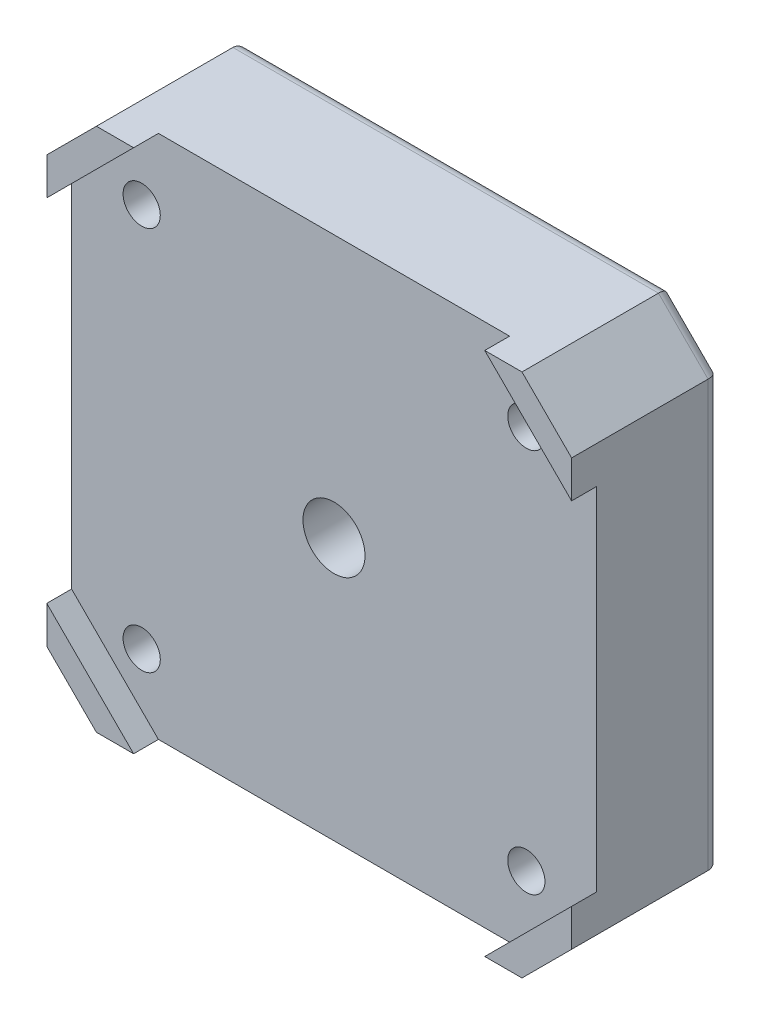
SolidWorks part; units mm, degrees
ref_plane "Ön Düzlem" through (0, 0, 0) normal (0, 0, 1) x (1, 0, 0)
ref_plane "Üst Düzlem" through (0, 0, 0) normal (0, 1, 0) x (1, 0, 0)
ref_plane "Sağ Düzlem" through (0, 0, 0) normal (1, 0, 0) x (0, 0, -1)
sketch "Çizim1" plane through (0, 0, 0) normal (0, 0, 1) x (1, 0, 0)
  line L0 (0, 38.3) -> (4, 42.3)
  line L1 (4, 42.3) -> (38.3, 42.3)
  line L2 (0, 38.3) -> (0, 4)
  line L3 (4, 0) -> (38.3, 0)
  line L4 (42.3, 38.3) -> (42.3, 4)
  line L5 (38.3, 42.3) -> (42.3, 38.3)
  line L6 (38.3, 0) -> (42.3, 4)
  line L7 (0, 4) -> (4, 0)
  point P0 (0, 42.3)
  point P1 (42.3, 0)
  point P2 (0, 0)
  point P3 (42.3, 42.3)
  dimension "D1" = 42.3
  dimension "D2" = 42.3
extrude "Yükseklik-Ekstrüzyon1" add sketch "Çizim1" along normal blind 12
sketch "Çizim2" plane through (0, 0, 12) normal (0, 0, 1) x (1, 0, 0)
  line L0 (0, 35.3) -> (7, 42.3)
  line L1 (7, 0) -> (35.3, 0)
  line L2 (0, 7) -> (0, 35.3)
  line L3 (7, 42.3) -> (35.3, 42.3)
  line L4 (42.3, 7) -> (42.3, 35.3)
  line L5 (35.3, 42.3) -> (42.3, 35.3)
  line L6 (35.3, 0) -> (42.3, 7)
  line L7 (0, 7) -> (7, 0)
  point P0 (0, 0)
  point P1 (42.3, 42.3)
  point P2 (0, 42.3)
  point P3 (42.3, 0)
  dimension "D1" = 42.3
  dimension "D2" = 42.3
extrude "Kes-Ekstrüzyon1" cut sketch "Çizim2" against normal blind 2
sketch "Çizim3" plane through (0, 0, 10) normal (0, 0, 1) x (1, 0, 0)
  line L0 (21.15, 0) -> (21.15, 42.3) construction
  line L1 (7, 0) -> (35.3, 0) construction
  line L2 (35.3, 42.3) -> (7, 42.3) construction
  line L3 (21.15, 21.15) -> (0, 21.15) construction
  line L4 (0, 35.3) -> (0, 7) construction
  line L5 (0, 21.15) -> (42.3, 21.15) construction
  line L6 (42.3, 7) -> (42.3, 35.3) construction
  line L8 (5.65, 36.65) -> (36.65, 36.65)
  line L9 (5.65, 36.65) -> (5.65, 5.65)
  line L10 (5.65, 5.65) -> (36.65, 5.65)
  line L11 (36.65, 36.65) -> (36.65, 5.65)
  line L12 (5.65, 36.65) -> (36.65, 5.65) construction
  line L13 (5.65, 5.65) -> (36.65, 36.65) construction
  circle A0 centre (5.65, 36.65) radius 1.5
  circle A1 centre (36.65, 36.65) radius 1.5
  circle A2 centre (36.65, 5.65) radius 1.5
  circle A3 centre (5.65, 5.65) radius 1.5
  dimension "D3" = 3
  dimension "D4" = 3
  dimension "D5" = 3
  dimension "D6" = 3
  dimension "D1" = 31
  dimension "D2" = 31
extrude "Kes-Ekstrüzyon2" cut sketch "Çizim3" against normal through all contours A0 | A1 | A2 | A3
sketch "Çizim5" plane through (0, 0, 0) normal (0, 0, -1) x (-1, 0, 0)
  line L1 (-36.65, 36.65) -> (-5.65, 36.65) construction
  line L2 (-36.65, 36.65) -> (-36.65, 5.65) construction
  line L3 (-36.65, 5.65) -> (-5.65, 5.65) construction
  line L4 (-5.65, 36.65) -> (-5.65, 5.65) construction
  circle A0 centre (-36.65, 36.65) radius 3.1
  circle A1 centre (-5.65, 36.65) radius 3.1
  circle A2 centre (-5.65, 5.65) radius 3.1
  circle A3 centre (-36.65, 5.65) radius 3.1
  dimension "D1" = 6.2
  dimension "D2" = 6.2
  dimension "D3" = 6.2
  dimension "D4" = 6.2
extrude "Kes-Ekstrüzyon3" cut sketch "Çizim5" against normal blind 3
fillet "Radyus1" radius 0.5 4 edges at (33.55, 5.65, 0) (2.55, 5.65, 0) (2.55, 36.65, 0) (33.55, 36.65, 0)
fillet "Radyus2" radius 1 8 edges at (40.3, 2, 0) (21.15, 0, 0) (2, 2, 0) (0, 21.15, 0) (2, 40.3, 0) (21.15, 42.3, 0) (40.3, 40.3, 0) (42.3, 21.15, 0)
sketch "Çizim6" plane through (0, 0, 0) normal (0, 0, -1) x (-1, 0, 0)
  line L0 (-21.15, 41.3) -> (-21.15, 1) construction
  line L1 (-4.4142, 41.3) -> (-37.8858, 41.3) construction
  line L2 (-37.8858, 1) -> (-4.4142, 1) construction
  line L3 (-41.3, 21.15) -> (-1, 21.15) construction
  line L4 (-41.3, 37.8858) -> (-41.3, 4.4142) construction
  line L5 (-1, 4.4142) -> (-1, 37.8858) construction
  circle A0 centre (-21.15, 21.15) radius 5.5
  dimension "D1" = 11
extrude "Kes-Ekstrüzyon4" cut sketch "Çizim6" against normal blind 5
sketch "Çizim7" plane through (0, 0, 5) normal (0, 0, -1) x (-1, 0, 0)
  circle A0 centre (-21.15, 21.15) radius 2.5
  dimension "D1" = 5
extrude "Kes-Ekstrüzyon5" cut sketch "Çizim7" against normal through all
fillet "Radyus3" radius 1 2 edges at (15.65, 21.15, 0) (15.65, 21.15, 5)
